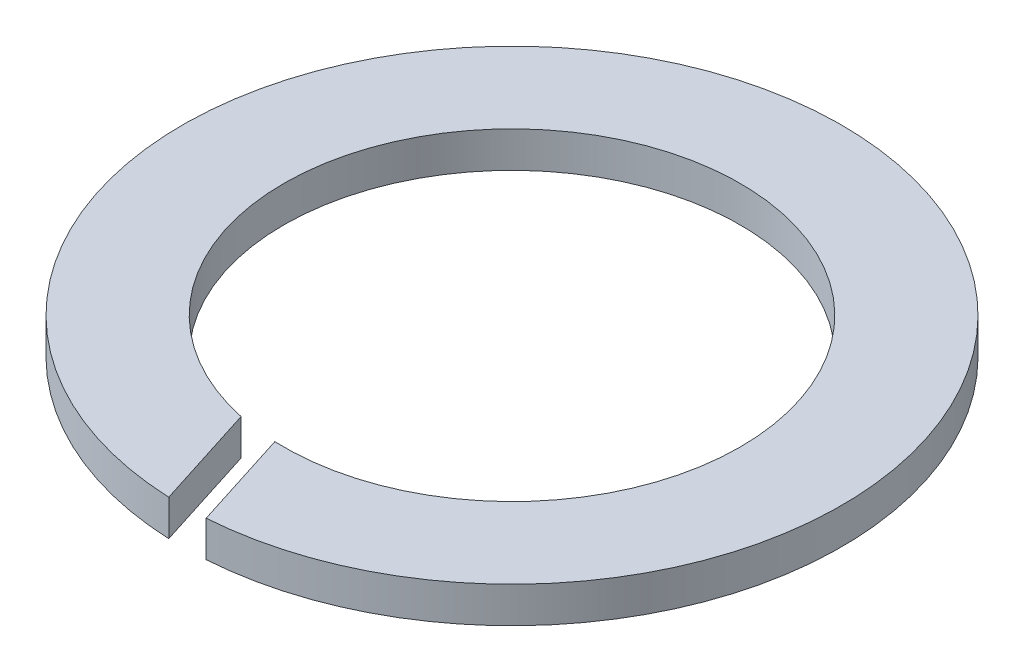
SolidWorks part; units mm, degrees
ref_plane "Alzado" through (0, 0, 0) normal (0, 0, 1) x (1, 0, 0)
ref_plane "Planta" through (0, 0, 0) normal (0, 1, 0) x (1, 0, 0)
ref_plane "Vista lateral" through (0, 0, 0) normal (1, 0, 0) x (0, 0, -1)
sketch "Croquis1" plane through (0, 0, 0) normal (0, 1, 0) x (1, 0, 0)
  circle A0 centre (0, 0) radius 19.05
  circle A1 centre (0, 0) radius 27.5
  dimension "D1" = 38.1
  dimension "D2" = 55
extrude "Saliente-Extruir1" add sketch "Croquis1" along normal blind 3
sketch "Croquis2" plane through (0, 3, 0) normal (0, 1, 0) x (1, 0, 0)
  line L0 (-1.1708, -27.4751) -> (-3.981, -18.6294)
  line L1 (-3.981, -18.6294) -> (-1.1708, -17.7367)
  line L2 (-1.1708, -17.7367) -> (2.3348, -28.7717)
  line L3 (2.3348, -28.7717) -> (-0.4753, -29.6644)
  line L4 (-0.4753, -29.6644) -> (-1.1708, -27.4751)
  circle A0 centre (0, 0) radius 27.5 construction
  circle A1 centre (0, 0) radius 19.05 construction
extrude "Cortar-Extruir1" cut sketch "Croquis2" against normal blind 3
